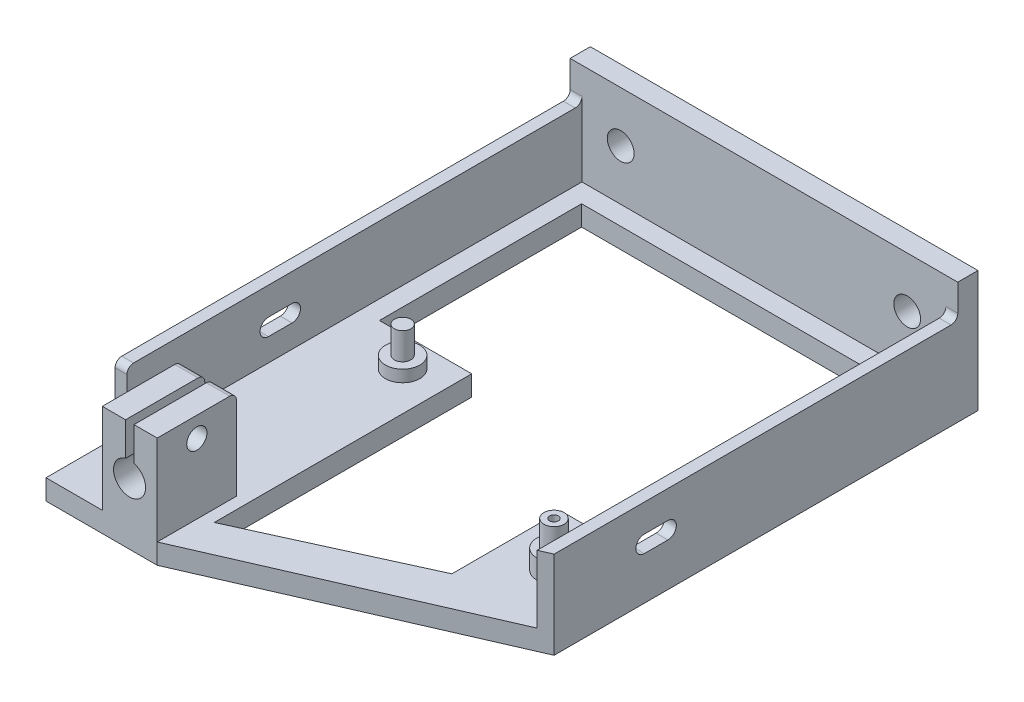
SolidWorks part; units mm, degrees
ref_plane "Front Plane" through (0, 0, 0) normal (0, 0, 1) x (1, 0, 0)
ref_plane "Top Plane" through (0, 0, 0) normal (0, 1, 0) x (1, 0, 0)
ref_plane "Right Plane" through (0, 0, 0) normal (1, 0, 0) x (0, 0, -1)
sketch "Sketch1" plane through (0, 0, 0) normal (0, 1, 0) x (1, 0, 0)
  line L1 (-57.5, -85) -> (57.5, -85)
  line L2 (-57.5, -85) -> (-57.5, 85)
  line L3 (-57.5, 85) -> (57.5, 85)
  line L4 (57.5, -85) -> (57.5, 85)
  line L5 (-57.5, -85) -> (57.5, 85) construction
  line L6 (-57.5, 85) -> (57.5, -85) construction
  point P0 (0, 0)
  dimension "D1" = 115
  dimension "D2" = 170
extrude "Back Wall Extrude" add sketch "Sketch1" along normal blind 6
sketch "Sketch2" plane through (0, 6, 0) normal (0, 1, 0) x (1, 0, 0)
  line L0 (57.5, -85) -> (57.5, 85) construction
  line L1 (-57.5, 85) -> (57.5, 85)
  line L2 (-57.5, 85) -> (-57.5, 79)
  line L3 (-57.5, 79) -> (57.5, 79)
  line L4 (57.5, 85) -> (57.5, 79)
  dimension "D1" = 6
extrude "Bottom Plate Extrude" add sketch "Sketch2" along normal blind 30
sketch "Sketch3" plane through (0, 6, 0) normal (0, 1, 0) x (1, 0, 0)
  line L1 (-57.5, 79) -> (-54, 79)
  line L2 (-57.5, 79) -> (-57.5, -56)
  line L3 (-57.5, -56) -> (-54, -56)
  line L4 (-54, 79) -> (-54, -56)
  line L5 (57.5, 79) -> (54, 79)
  line L6 (57.5, 79) -> (57.5, -56)
  line L7 (57.5, -56) -> (54, -56)
  line L8 (54, 79) -> (54, -56)
  dimension "D1" = 135
  dimension "D2" = 3.5
  dimension "D3" = 3.5
  dimension "D7" = 135
extrude "Side Walls Extrude" add sketch "Sketch3" along normal blind 20
sketch "Sketch4" plane through (0, 6, 0) normal (0, 1, 0) x (1, 0, 0)
  line L2 (-40.8, -76.5) -> (-40.8, -53)
  line L3 (-40.8, -53) -> (-24.5, -53)
  line L4 (-24.5, -76.5) -> (-24.5, -53)
  line L5 (-57.5, -56) -> (-57.5, -85) construction
  line L6 (-40.8, -76.5) -> (-24.5, -76.5)
  line L8 (-57.5, -85) -> (57.5, -85) construction
  dimension "D1" = 33
  dimension "D2" = 16.3
  dimension "D3" = 23.5
  dimension "D4" = 32
extrude "Dial Indiactor Holder Extrude" add sketch "Sketch4" along normal blind 26.7
sketch "Sketch6" plane through (-40.8, 0, 0) normal (-1, 0, 0) x (0, 0, 1)
  line L1 (53, 32.7) -> (53, 6) construction
  line L3 (53, 32.7) -> (76.5, 32.7) construction
  circle A0 centre (64.75, 26.7) radius 3
  dimension "D1" = 11.75
  dimension "D3" = 6
  dimension "D2" = 6
extrude "Dial Indicator Tightener Hole Cut" cut sketch "Sketch6" against normal blind 26.7
sketch "Sketch7" plane through (0, 6, 0) normal (0, 1, 0) x (1, 0, 0)
  line L0 (-54, 79) -> (54, 79) construction
  line L1 (57.5, -56) -> (57.5, 79) construction
  circle A0 centre (41.6, -24.9) radius 5.1
  dimension "D1" = 10.2
  dimension "D3" = 15.9
  dimension "D2" = 103.9
sketch "Sketch18" plane through (0, 0, 76.5) normal (0, 0, 1) x (1, 0, 0)
  line L0 (-40.8, 32.7) -> (-24.5, 32.7) construction
  line L1 (-33.9, 32.7) -> (-31.4, 32.7)
  line L2 (-33.9, 32.7) -> (-33.9, 22.7989)
  line L4 (-31.4, 32.7) -> (-31.4, 22.7653)
  line L5 (-24.5, 32.7) -> (-24.5, 6) construction
  arc A0 (-33.9, 22.7989) -> (-31.4, 22.7653) centre (-32.7116, 18.2) ccw
  dimension "D4" = 9.5
  dimension "D1" = 6.9
  dimension "D2" = 2.5
  dimension "D3" = 14.5
extrude "Dial Indicator Holder Cut" cut sketch "Sketch18" against normal blind 30
extrude "Arm Base Extrude" add sketch "Sketch7" along normal blind 5.7
sketch "Sketch8" plane through (0, 11.7, 0) normal (0, 1, 0) x (1, 0, 0)
  circle A0 centre (41.6, -24.9) radius 3
extrude "Arm Axle Extrude" add sketch "Sketch8" along normal blind 7.6
sketch "Sketch9" plane through (0, 6, 0) normal (0, 1, 0) x (1, 0, 0)
  line L0 (-57.5, 79) -> (-57.5, -56) construction
  line L1 (57.5, 85) -> (-57.5, 85) construction
  circle A0 centre (-32.6, 4.4) radius 5.1
  dimension "D1" = 10.2
  dimension "D2" = 24.9
  dimension "D3" = 80.6
extrude "Guide Wheel Base Extrude" add sketch "Sketch9" along normal blind 3.5
sketch "Sketch10" plane through (0, 9.5, 0) normal (0, 1, 0) x (1, 0, 0)
  circle A0 centre (-32.6, 4.4) radius 2.45
  dimension "D1" = 4.9
extrude "Guide Wheel Axle Extrude" add sketch "Sketch10" along normal blind 8
sketch "Sketch11" plane through (-57.5, 0, 0) normal (-1, 0, 0) x (0, 0, 1)
  line L0 (14, 15.2656) -> (7, 15.2656) construction
  line L1 (14, 12.7656) -> (7, 12.7656)
  line L2 (14, 17.7656) -> (7, 17.7656)
  line L3 (-85, 36) -> (-85, 0) construction
  line L5 (-85, 0) -> (85, 0) construction
  arc A0 (14, 12.7656) -> (14, 17.7656) centre (14, 15.2656) ccw
  arc A1 (7, 17.7656) -> (7, 12.7656) centre (7, 15.2656) ccw
  point P2 (10.5, 15.2656)
  dimension "D2" = 2.5
  dimension "D1" = 92
  dimension "D3" = 7
  dimension "D4" = 12.7656
extrude "Filament Slot Cut" cut sketch "Sketch11" against normal through all
sketch "Sketch13" plane through (0, 0, -85) normal (0, 0, -1) x (-1, 0, 0)
  line L0 (57.5, 36) -> (-57.5, 36) construction
  line L1 (57.5, 36) -> (57.5, 26) construction
  line L2 (-57.5, 36) -> (-57.5, 26) construction
  circle A0 centre (42.5, 21) radius 3.9687
  circle A1 centre (-42.5, 21) radius 3.9687
  dimension "D2" = 7.9375
  dimension "D3" = 7.9375
  dimension "D1" = 15
  dimension "D4" = 15
  dimension "D5" = 15
extrude "Mounting Holes Cut" cut sketch "Sketch13" against normal blind 8
fillet "Fillet1" radius 2 7 edges at (55.75, 26, 56) (-55.75, 26, 56) (-27.95, 32.7, 53) (-37.35, 32.7, 53) (55.75, 26, -79) (-55.75, 26, -79) (-57.5, 3, 85)
sketch "Sketch15" plane through (0, 19.3, 0) normal (0, 1, 0) x (1, 0, 0)
  circle A0 centre (41.6, -24.9) radius 1.3
  dimension "D1" = 2.6
extrude "Screw Hole Cut" cut sketch "Sketch15" against normal through all
sketch "Sketch21" plane through (0, 6, 0) normal (0, 1, 0) x (1, 0, 0)
  line L1 (-48.4461, 73.3483) -> (48.8989, 73.3483)
  line L2 (-48.4461, 73.3483) -> (-48.4461, 13.3566)
  line L3 (-48.4461, 13.3566) -> (-21.0537, 13.3566)
  line L4 (48.8989, 73.3483) -> (48.8989, 13.3566)
  line L11 (-21.0537, 13.3566) -> (-21.0537, -63.0349)
  line L13 (27.3924, -8.6397) -> (27.3924, -40.9754)
  line L20 (27.3924, -8.6397) -> (48.8989, -8.6397)
  line L21 (48.8989, 13.3566) -> (48.8989, -8.6397)
  line L22 (27.3924, -40.9754) -> (-21.0537, -63.0349)
extrude "Weight Reduction Cut" cut sketch "Sketch21" against normal up to next
sketch "Sketch22" plane through (0, 6, 0) normal (0, 1, 0) x (1, 0, 0)
  line L0 (57.5, -40.7491) -> (-24.5, -76.5)
  line L1 (57.5, -54) -> (57.5, 77) construction
  line L2 (-24.5, -76.5) -> (-57.5, -76.5)
  line L3 (-57.5, -56) -> (-57.5, -83) construction
  line L4 (-57.5, -76.5) -> (-57.5, -85)
  line L5 (-57.5, -85) -> (57.5, -85)
  line L6 (57.5, -85) -> (57.5, -40.7491)
extrude "Weight Reduction Cut 2" cut sketch "Sketch22" against normal mid plane 40
